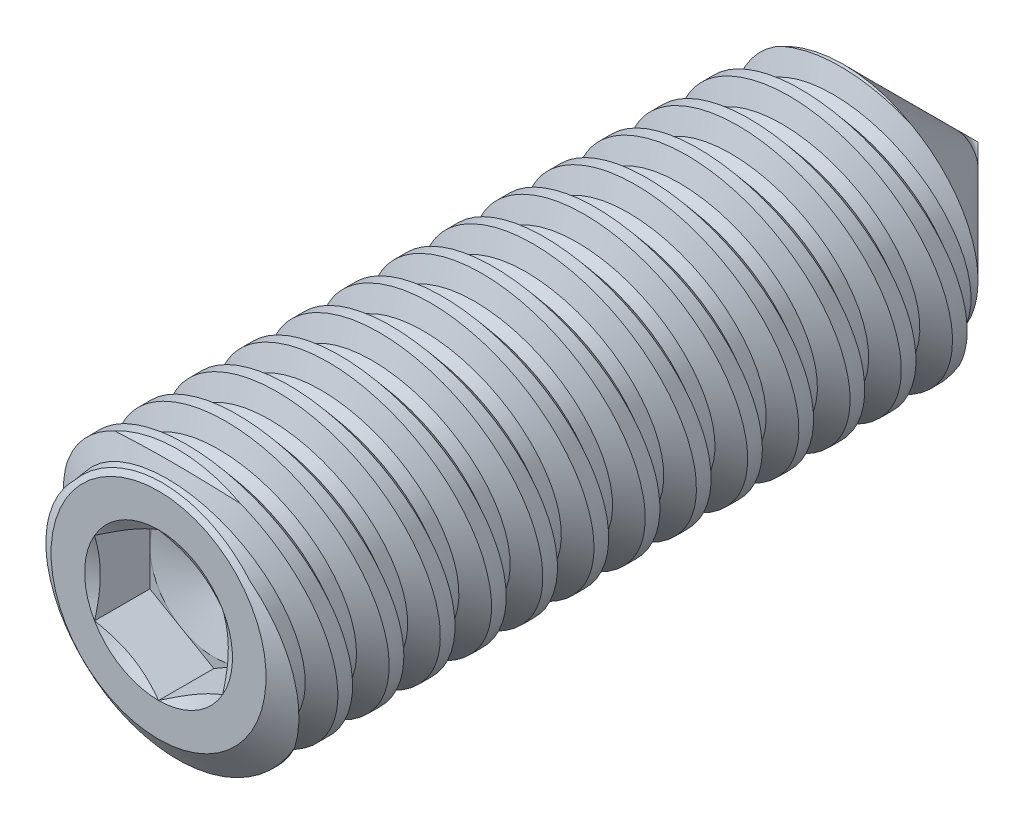
SolidWorks part; units mm, degrees
ref_plane "Front" through (0, 0, 0) normal (0, 0, 1) x (1, 0, 0)
ref_plane "Top" through (0, 0, 0) normal (0, 1, 0) x (1, 0, 0)
ref_plane "Right" through (0, 0, 0) normal (1, 0, 0) x (0, 0, -1)
sketch "Sketch22" plane through (0, 0, 0) normal (1, 0, 0) x (0, 0, -1)
  line L0 (-6.35, 0) -> (-6.35, 1.6662)
  line L1 (-6.35, 1.6662) -> (-6.0583, 2.0828)
  line L2 (-6.0583, 2.0828) -> (4.2672, 2.0828)
  line L3 (4.2672, 2.0828) -> (6.35, 2.0828) construction
  line L4 (4.2672, 2.0828) -> (6.35, 0)
  line L5 (6.35, 0) -> (-6.35, 0)
  line L6 (6.8585, 0) -> (6.35, 0) construction
  line L7 (6.35, 0) -> (6.35, 2.0828) construction
  line L8 (4.2672, -2.0828) -> (6.35, 0) construction
  line L10 (6.35, -2.0828) -> (-6.35, -2.0828) construction
  line L11 (-6.35, -2.0828) -> (-6.35, 0) construction
  line L12 (0, -2.0828) -> (0, 0) construction
  dimension "D1" = 10.6172
  dimension "Screw Dia" = 4.1656
  dimension "Length" = 12.7
  dimension "D3" = 35
  dimension "D7" = 3.3325
  dimension "Cone Point" = 90
revolve "Revolve1" add sketch "Sketch22" angle 360 about L6
sketch "Sketch6" plane through (0, 0, 0) normal (1, 0, 0) x (0, 0, -1)
  line L0 (3.4875, 2.0828) -> (4.2812, -2.0828) construction
  line L1 (-6.0583, 2.0828) -> (4.2672, 2.0828) construction
  line L2 (4.2672, 2.0828) -> (4.2672, 2.2314) construction
  line L3 (3.4875, 2.0828) -> (3.5849, 2.1014) construction
  line L4 (4.104, 1.7629) -> (3.909, 1.7258)
  line L5 (3.909, 1.7258) -> (3.5849, 2.1014)
  line L6 (4.104, 1.7629) -> (4.2672, 2.2314)
  line L7 (4.2672, 2.2314) -> (3.5849, 2.1014)
  line L8 (3.942, 2.0828) -> (4.7357, -2.0828) construction
  line L9 (5.1903, 0.1622) -> (3.4875, -0.1622) construction
  line L10 (3.9261, 2.1664) -> (4.0065, 1.7443) construction
  line L12 (6.35, -2.0828) -> (-6.35, -2.0828) construction
  line L13 (3.4875, -2.0828) -> (3.4875, 2.0828) construction
  line L14 (3.4875, -2.0828) -> (4.2812, -2.0828) construction
  line L15 (4.2812, -2.0828) -> (4.7357, -2.0828) construction
  line L18 (3.4875, 2.0828) -> (3.942, 2.0828) construction
  point P18 (4.3389, 0)
  dimension "D1" = 0.7937
  dimension "D2" = 0.1984
  dimension "D3" = 60
  dimension "D4" = 0.0992
  dimension "Pitch" = 0.7937
revolve "Cut-Revolve8" cut sketch "Sketch6" angle 360 about L9
pattern_linear "LPattern1" count 14 spacing 0.7937 along (0, 0, 1) count 2 spacing 0.7937 along (0, 0, 1) of "Cut-Revolve8"
sketch "Sketch23" plane through (0, 0, 6.35) normal (0, 0, 1) x (1, 0, 0)
  line L1 (0, 1.1457) -> (-0.9922, 0.5728)
  line L2 (-0.9922, 0.5728) -> (-0.9922, -0.5728)
  line L3 (-0.9922, -0.5728) -> (0, -1.1457)
  line L4 (0, -1.1457) -> (0.9922, -0.5728)
  line L5 (0.9922, -0.5728) -> (0.9922, 0.5728)
  line L6 (0.9922, 0.5728) -> (0, 1.1457)
  circle A0 centre (0, 0) radius 0.9922 construction
  dimension "Hex" = 1.9844
extrude "Cut-Extrude10" cut sketch "Sketch23" against normal blind 0.8573
sketch "Sketch24" plane through (0, 0, 6.35) normal (0, 0, 1) x (1, 0, 0)
  circle A0 centre (0, 0) radius 1.1457
extrude "Cut-Extrude11" cut sketch "Sketch24" against normal through all draft 60
sketch "Sketch26" plane through (0, 0, 5.4927) normal (0, 0, 1) x (1, 0, 0)
  circle A0 centre (0, 0) radius 0.9922 construction
  circle A1 centre (0, 0) radius 0.9922
extrude "Cut-Extrude12" cut sketch "Sketch26" against normal through all draft 75
sketch "Sketch27" plane through (0, 0, 0) normal (1, 0, 0) x (0, 0, -1)
  line L0 (6.35, 0) -> (6.368, 0.018) construction
  line L1 (6.35, 0) -> (6.368, -0.018) construction
  line L2 (6.8585, 0) -> (6.35, 0) construction
  line L3 (4.2672, 2.0828) -> (6.35, 0) construction
  line L4 (4.2672, -2.0828) -> (6.35, 0) construction
  dimension "D1" = 0.0254
equation "\"D2@Sketch6\"=\"Pitch@Sketch6\"/4"
equation "\"D4@Sketch6\"=\"Pitch@Sketch6\"/8"
equation "\"D1@Sketch6\"=\"Pitch@Sketch6\""
equation "\"D3@LPattern1\"=\"Pitch@Sketch6\""
equation "\"D1@LPattern1\"=(\"D1@Sketch22\"/\"Pitch@Sketch6\")+1"
equation "\"D4@LPattern1\"=\"Pitch@Sketch6\""
equation "\"D7@Sketch22\"=\"Screw Dia@Sketch22\"*.8"
